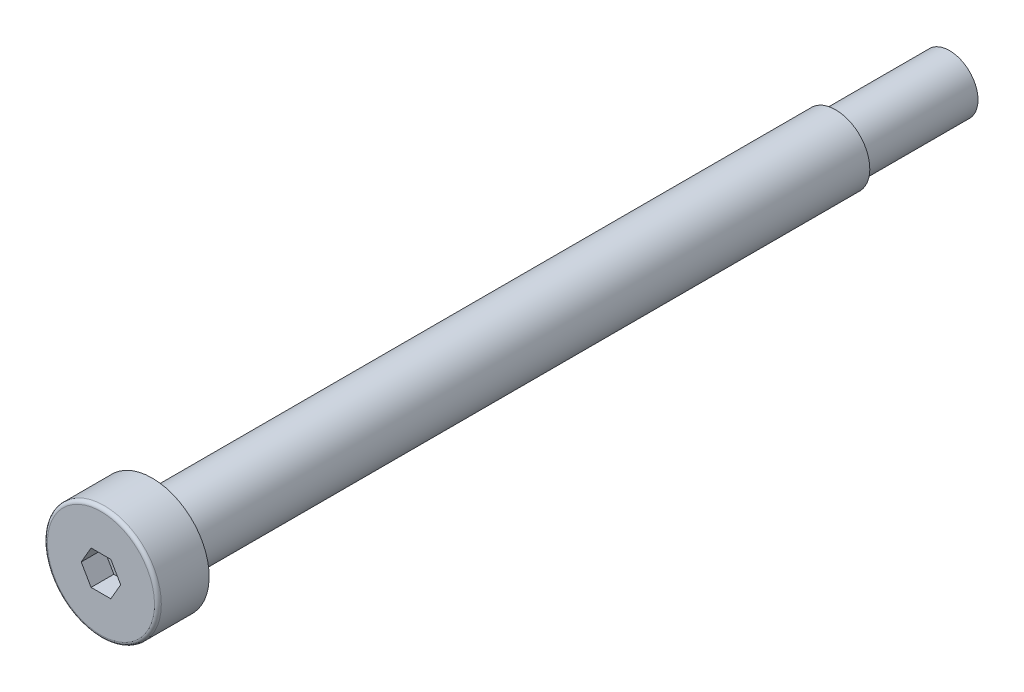
SolidWorks part; units mm, degrees
material "普通碳钢"
ref_plane "前视基准面" through (0, 0, 0) normal (0, 0, 1) x (1, 0, 0)
ref_plane "上视基准面" through (0, 0, 0) normal (0, 1, 0) x (1, 0, 0)
ref_plane "右视基准面" through (0, 0, 0) normal (1, 0, 0) x (0, 0, -1)
sketch "草图1" plane through (0, 0, 0) normal (1, 0, 0) x (0, 0, -1)
  line L0 (0, 0) -> (0, 5)
  line L1 (0, 5) -> (4.5, 5)
  line L2 (4.5, 5) -> (4.5, 3)
  line L3 (4.5, 3) -> (64.5, 3)
  line L4 (64.5, 3) -> (64.5, 2.5)
  line L5 (64.5, 2.5) -> (74.5, 2.5)
  line L6 (74.5, 2.5) -> (74.5, 0)
  line L7 (74.5, 0) -> (0, 0) construction
  line L8 (0, 0) -> (74.5, 0)
  dimension "头部直径" = 10
  dimension "头部厚度" = 4.5
  dimension "光杆长度" = 60
  dimension "光杆直径" = 6
  dimension "螺纹直径" = 5
  dimension "螺纹长度" = 10
revolve "旋转1" add sketch "草图1" angle 360 about L7
cosmetic thread "装饰螺纹线1" parameters "D2"=4
sketch "草图2" plane through (0, 0, 0) normal (0, 0, 1) x (1, 0, 0)
  line L1 (0.866, 1.5) -> (-0.866, 1.5)
  line L2 (-0.866, 1.5) -> (-1.7321, 0)
  line L3 (-1.7321, 0) -> (-0.866, -1.5)
  line L4 (-0.866, -1.5) -> (0.866, -1.5)
  line L5 (0.866, -1.5) -> (1.7321, 0)
  line L6 (1.7321, 0) -> (0.866, 1.5)
  circle A0 centre (0, 0) radius 1.5 construction
  dimension "对边长度" = 3
extrude "切除-拉伸1" cut sketch "草图2" against normal blind 2
fillet "圆角1" radius 0.3 1 edges at (0, 5, 0)
